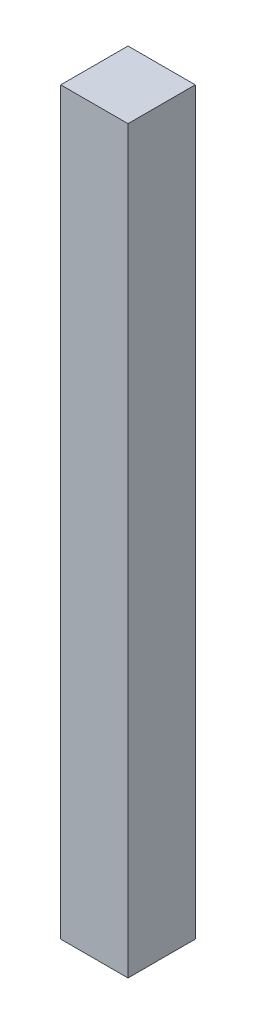
SolidWorks part; units mm, degrees
ref_plane "Front Plane" through (0, 0, 0) normal (0, 0, 1) x (1, 0, 0)
ref_plane "Top Plane" through (0, 0, 0) normal (0, 1, 0) x (1, 0, 0)
ref_plane "Right Plane" through (0, 0, 0) normal (1, 0, 0) x (0, 0, -1)
sketch "Sketch1" plane through (0, 0, 0) normal (0, 1, 0) x (1, 0, 0)
  line L1 (0, 0) -> (25.4, 0)
  line L2 (0, 0) -> (0, 25.4)
  line L3 (0, 25.4) -> (25.4, 25.4)
  line L4 (25.4, 0) -> (25.4, 25.4)
  dimension "D1" = 25.4
  dimension "D2" = 25.4
extrude "Boss-Extrude1" add sketch "Sketch1" along normal blind 279.4
